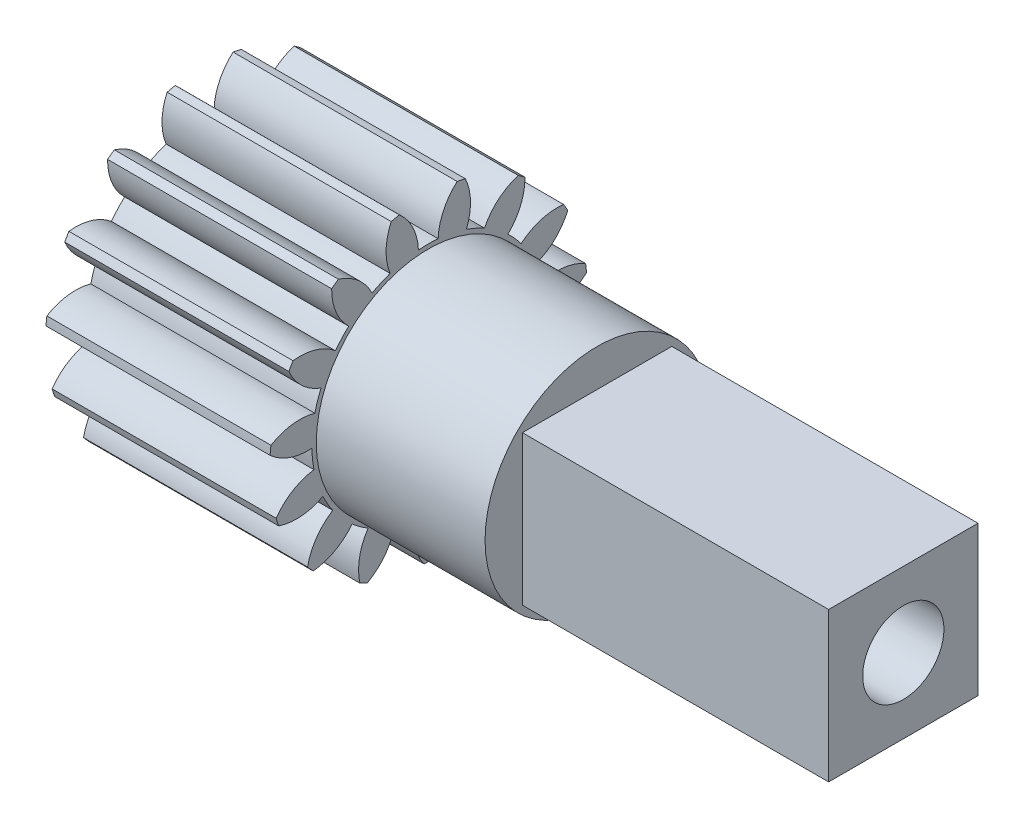
SolidWorks part; units mm, degrees
material "AISI 4130 Steel, annealed at 865C"
ref_plane "Front Plane" through (0, 0, 0) normal (0, 0, 1) x (1, 0, 0)
ref_plane "Top Plane" through (0, 0, 0) normal (0, 1, 0) x (1, 0, 0)
ref_plane "Right Plane" through (0, 0, 0) normal (1, 0, 0) x (0, 0, -1)
ref_plane "Plane1" through (0, 0, 0) normal (0, 0, -1) x (-1, 0, 0)
sketch "Sketch1" plane through (0, 0, 0) normal (0, 0, -1) x (-1, 0, 0)
  line L0 (-6.35, 6.7469) -> (-6.35, 0)
  line L1 (-6.35, 0) -> (3.175, 0)
  line L2 (3.175, 0) -> (3.175, 6.7469)
  line L3 (3.175, 6.7469) -> (-6.35, 6.7469)
  line L4 (-6.35, 0) -> (3.175, 0) construction
revolve "Revolve1" add sketch "Sketch1" angle 360 about L4
sketch "Sketch2" plane through (6.35, 0, 0) normal (1, 0, 0) x (0, 0, -1)
  arc A0 (-4.8934, -4.6449) -> (-2.9054, -6.0892) centre (0, 0) ccw
  arc A1 (-2.9054, -6.0892) -> (-2.56, -4.2364) centre (-0.5829, -5.5637) cw
  arc A2 (-2.56, -4.2364) -> (-3.238, -3.7438) centre (0, 0) cw
  arc A3 (-3.238, -3.7438) -> (-4.8934, -4.6449) centre (-5.1112, -2.2737) cw
extrude "Cut-Extrude1" cut sketch "Sketch2" against normal through all
sketch "Sketch3" plane through (6.35, 0, 0) normal (1, 0, 0) x (0, 0, -1)
  arc A0 (-6.3596, -2.253) -> (-5.131, -4.381) centre (0, 0) ccw
  arc A1 (-5.131, -4.381) -> (-4.0618, -2.8289) centre (-2.7955, -4.8456) cw
  arc A2 (-4.0618, -2.8289) -> (-4.4808, -2.1031) centre (0, 0) cw
  arc A3 (-4.4808, -2.1031) -> (-6.3596, -2.253) centre (-5.5941, 0.0018) cw
extrude "Cut-Extrude2" cut sketch "Sketch3" against normal through all
sketch "Sketch4" plane through (6.35, 0, 0) normal (1, 0, 0) x (0, 0, -1)
  arc A0 (-6.7261, 0.5284) -> (-6.4693, -1.9153) centre (0, 0) ccw
  arc A1 (-6.4693, -1.9153) -> (-4.8612, -0.9323) centre (-4.5247, -3.2896) cw
  arc A2 (-4.8612, -0.9323) -> (-4.9488, -0.0988) centre (0, 0) cw
  arc A3 (-4.9488, -0.0988) -> (-6.7261, 0.5284) centre (-5.1097, 2.277) cw
extrude "Cut-Extrude3" cut sketch "Sketch4" against normal through all
sketch "Sketch5" plane through (6.35, 0, 0) normal (1, 0, 0) x (0, 0, -1)
  arc A0 (-5.9297, 3.2185) -> (-6.689, 0.8816) centre (0, 0) ccw
  arc A1 (-6.689, 0.8816) -> (-4.8202, 1.1256) centre (-5.4715, -1.1649) cw
  arc A2 (-4.8202, 1.1256) -> (-4.5612, 1.9226) centre (0, 0) cw
  arc A3 (-4.5612, 1.9226) -> (-5.9297, 3.2185) centre (-3.7418, 4.1585) cw
extrude "Cut-Extrude4" cut sketch "Sketch5" against normal through all
sketch "Sketch6" plane through (6.35, 0, 0) normal (1, 0, 0) x (0, 0, -1)
  arc A0 (-5.7522, 3.526) -> (-3.9456, 2.9888) centre (-5.4722, 1.1613) cw
  arc A1 (-3.9456, 2.9888) -> (-3.3848, 3.6116) centre (0, 0) cw
  arc A2 (-3.3848, 3.6116) -> (-4.108, 5.3521) centre (-1.7269, 5.3209) cw
  arc A3 (-4.108, 5.3521) -> (-5.7522, 3.526) centre (0, 0) ccw
extrude "Cut-Extrude5" cut sketch "Sketch6" against normal through all
sketch "Sketch7" plane through (6.35, 0, 0) normal (1, 0, 0) x (0, 0, -1)
  arc A0 (-3.8207, 5.5608) -> (-2.3889, 4.3352) centre (-4.5268, 3.2867) cw
  arc A1 (-2.3889, 4.3352) -> (-1.6232, 4.6761) centre (0, 0) cw
  arc A2 (-1.6232, 4.6761) -> (-1.5759, 6.5602) centre (0.5866, 5.5633) cw
  arc A3 (-1.5759, 6.5602) -> (-3.8207, 5.5608) centre (0, 0) ccw
extrude "Cut-Extrude6" cut sketch "Sketch7" against normal through all
sketch "Sketch8" plane through (6.35, 0, 0) normal (1, 0, 0) x (0, 0, -1)
  arc A0 (1.2286, 6.6341) -> (-1.2286, 6.6341) centre (0, 0) ccw
  arc A1 (-1.2286, 6.6341) -> (-0.419, 4.9321) centre (-2.7986, 4.8437) cw
  arc A2 (-0.419, 4.9321) -> (0.419, 4.9321) centre (0, 0) cw
  arc A3 (0.419, 4.9321) -> (1.2286, 6.6341) centre (2.7986, 4.8437) cw
extrude "Cut-Extrude7" cut sketch "Sketch8" against normal through all
sketch "Sketch9" plane through (6.35, 0, 0) normal (1, 0, 0) x (0, 0, -1)
  arc A0 (3.8207, 5.5608) -> (1.5759, 6.5602) centre (0, 0) ccw
  arc A1 (1.5759, 6.5602) -> (1.6232, 4.6761) centre (-0.5866, 5.5633) cw
  arc A2 (1.6232, 4.6761) -> (2.3889, 4.3352) centre (0, 0) cw
  arc A3 (2.3889, 4.3352) -> (3.8207, 5.5608) centre (4.5268, 3.2867) cw
extrude "Cut-Extrude8" cut sketch "Sketch9" against normal through all
sketch "Sketch10" plane through (6.35, 0, 0) normal (1, 0, 0) x (0, 0, -1)
  arc A0 (5.7522, 3.526) -> (4.108, 5.3521) centre (0, 0) ccw
  arc A1 (4.108, 5.3521) -> (3.3848, 3.6116) centre (1.7269, 5.3209) cw
  arc A2 (3.3848, 3.6116) -> (3.9456, 2.9888) centre (0, 0) cw
  arc A3 (3.9456, 2.9888) -> (5.7522, 3.526) centre (5.4722, 1.1613) cw
extrude "Cut-Extrude9" cut sketch "Sketch10" against normal through all
sketch "Sketch11" plane through (6.35, 0, 0) normal (1, 0, 0) x (0, 0, -1)
  arc A0 (6.689, 0.8816) -> (5.9297, 3.2185) centre (0, 0) ccw
  arc A1 (5.9297, 3.2185) -> (4.5612, 1.9226) centre (3.7418, 4.1585) cw
  arc A2 (4.5612, 1.9226) -> (4.8202, 1.1256) centre (0, 0) cw
  arc A3 (4.8202, 1.1256) -> (6.689, 0.8816) centre (5.4715, -1.1649) cw
extrude "Cut-Extrude10" cut sketch "Sketch11" against normal through all
sketch "Sketch12" plane through (6.35, 0, 0) normal (1, 0, 0) x (0, 0, -1)
  arc A0 (6.4693, -1.9153) -> (6.7261, 0.5284) centre (0, 0) ccw
  arc A1 (6.7261, 0.5284) -> (4.9488, -0.0988) centre (5.1097, 2.277) cw
  arc A2 (4.9488, -0.0988) -> (4.8612, -0.9323) centre (0, 0) cw
  arc A3 (4.8612, -0.9323) -> (6.4693, -1.9153) centre (4.5247, -3.2896) cw
extrude "Cut-Extrude11" cut sketch "Sketch12" against normal through all
sketch "Sketch13" plane through (6.35, 0, 0) normal (1, 0, 0) x (0, 0, -1)
  arc A0 (5.131, -4.381) -> (6.3596, -2.253) centre (0, 0) ccw
  arc A1 (6.3596, -2.253) -> (4.4808, -2.1031) centre (5.5941, 0.0018) cw
  arc A2 (4.4808, -2.1031) -> (4.0618, -2.8289) centre (0, 0) cw
  arc A3 (4.0618, -2.8289) -> (5.131, -4.381) centre (2.7955, -4.8456) cw
extrude "Cut-Extrude12" cut sketch "Sketch13" against normal through all
sketch "Sketch14" plane through (6.35, 0, 0) normal (1, 0, 0) x (0, 0, -1)
  arc A0 (2.9054, -6.0892) -> (4.8934, -4.6449) centre (0, 0) ccw
  arc A1 (4.8934, -4.6449) -> (3.238, -3.7438) centre (5.1112, -2.2737) cw
  arc A2 (3.238, -3.7438) -> (2.56, -4.2364) centre (0, 0) cw
  arc A3 (2.56, -4.2364) -> (2.9054, -6.0892) centre (0.5829, -5.5637) cw
extrude "Cut-Extrude13" cut sketch "Sketch14" against normal through all
sketch "Sketch15" plane through (6.35, 0, 0) normal (1, 0, 0) x (0, 0, -1)
  arc A0 (0.1775, -6.7445) -> (2.5811, -6.2337) centre (0, 0) ccw
  arc A1 (2.5811, -6.2337) -> (1.4353, -4.7372) centre (3.7446, -4.156) cw
  arc A2 (1.4353, -4.7372) -> (0.6156, -4.9114) centre (0, 0) cw
  arc A3 (0.6156, -4.9114) -> (0.1775, -6.7445) centre (-1.7304, -5.3197) cw
extrude "Cut-Extrude14" cut sketch "Sketch15" against normal through all
sketch "Sketch16" plane through (6.35, 0, 0) normal (1, 0, 0) x (0, 0, -1)
  arc A0 (-2.5811, -6.2337) -> (-0.1775, -6.7445) centre (0, 0) ccw
  arc A1 (-0.1775, -6.7445) -> (-0.6156, -4.9114) centre (1.7304, -5.3197) cw
  arc A2 (-0.6156, -4.9114) -> (-1.4353, -4.7372) centre (0, 0) cw
  arc A3 (-1.4353, -4.7372) -> (-2.5811, -6.2337) centre (-3.7446, -4.156) cw
extrude "Cut-Extrude15" cut sketch "Sketch16" against normal through all
sketch "Sketch17" plane through (6.35, 0, 0) normal (1, 0, 0) x (0, 0, -1)
  circle A0 centre (0, 0) radius 4.7625
extrude "Boss-Extrude1" add sketch "Sketch17" along normal blind 7.1755
sketch "Sketch18" plane through (13.5255, 0, 0) normal (1, 0, 0) x (0, 0, -1)
  line L0 (-3.175, 3.175) -> (3.175, 3.175)
  line L1 (3.175, 3.175) -> (3.175, -3.175)
  line L2 (3.175, -3.175) -> (-3.175, -3.175)
  line L3 (-3.175, -3.175) -> (-3.175, 3.175)
extrude "Boss-Extrude2" add sketch "Sketch18" along normal blind 13.0175
hole_wizard "M3 Clearance Hole1" positions "Sketch20" profile "Sketch19" hole size "M3" standard "ANSI Metric"
sketch "Sketch20" plane through (26.543, 0, 0) normal (1, 0, 0) x (0, 0, -1)
  point P0 (0, 0)
sketch "Sketch19" plane through (26.543, 0, 0) normal (0, 1, 0) x (0, 0, -1)
  line L0 (0, 0) -> (0, 17.9694)
  line L1 (0, 17.9694) -> (1.7272, 16.9316)
  line L2 (1.7272, 16.9316) -> (1.7272, 0)
  line L5 (1.7272, 0) -> (0, 0)
  line L10 (0, 17.9694) -> (-1.7272, 16.9316) construction
  line L11 (0, -6.35) -> (0, 107.95) construction
  dimension "Hole Dia." = 3.4544
  dimension "Hole Depth" = 16.9316
  dimension "Drill Angle" = 118
